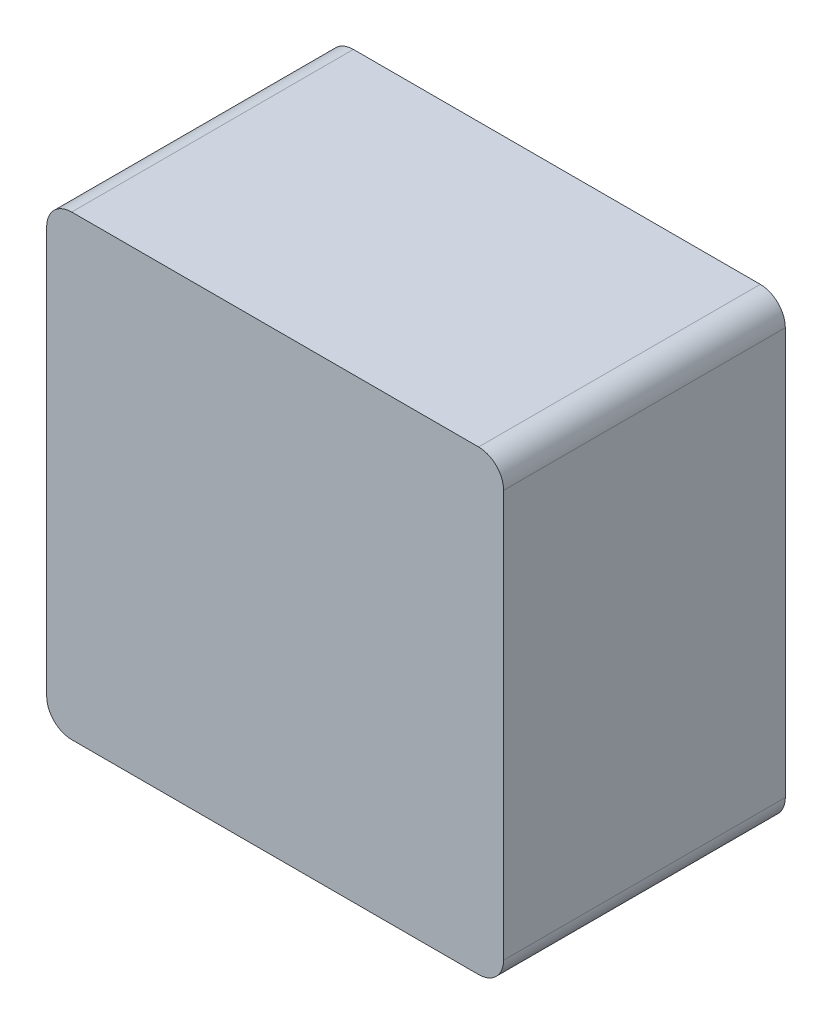
SolidWorks part; units mm, degrees
material "BUTYL"
ref_plane "Plan de face" through (0, 0, 0) normal (0, 0, 1) x (1, 0, 0)
ref_plane "Plan de dessus" through (0, 0, 0) normal (0, 1, 0) x (1, 0, 0)
ref_plane "Plan de droite" through (0, 0, 0) normal (1, 0, 0) x (0, 0, -1)
sketch "Esquisse1" plane through (0, 0, 0) normal (0, 0, 1) x (1, 0, 0)
  line L1 (-3.65, -3.65) -> (3.65, -3.65)
  line L2 (-3.65, -3.65) -> (-3.65, 3.65)
  line L3 (-3.65, 3.65) -> (3.65, 3.65)
  line L4 (3.65, -3.65) -> (3.65, 3.65)
  line L5 (-3.65, -3.65) -> (3.65, 3.65) construction
  line L6 (-3.65, 3.65) -> (3.65, -3.65) construction
  point P0 (0, 0)
  dimension "D1" = 7.3
  dimension "D2" = 7.3
extrude "Boss.-Extru.1" add sketch "Esquisse1" along normal blind 4.5
fillet "Congé1" radius 0.4 4 edges at (-3.65, -3.65, 2.25) (3.65, -3.65, 2.25) (3.65, 3.65, 2.25) (-3.65, 3.65, 2.25)
sketch "Esquisse2" plane through (0, 0, 0) normal (0, 0, -1) x (-1, 0, 0)
  circle A0 centre (0, 0) radius 3.194
extrude "Enlèv. mat.-Extru.1" cut sketch "Esquisse2" against normal blind 0.5
sketch "Esquisse4" plane through (0, 0, 0.5) normal (0, 0, -1) x (-1, 0, 0)
  circle A0 centre (0, 0) radius 2.7227
extrude "Boss.-Extru.2" add sketch "Esquisse4" along normal blind 0.5
fillet "Congé2" radius 0.1 1 edges at (-2.7227, 0, 0)
fillet "Congé3" radius 0.1 1 edges at (-3.194, 0, 0)
sketch "Esquisse5" plane through (0, 0, 0) normal (0, 0, -1) x (-1, 0, 0)
  text T0 "3.3uH" font "@Arial Unicode MS" height in points 3
extrude "Enlèv. mat.-Extru.2" cut sketch "Esquisse5" against normal blind 0.15
